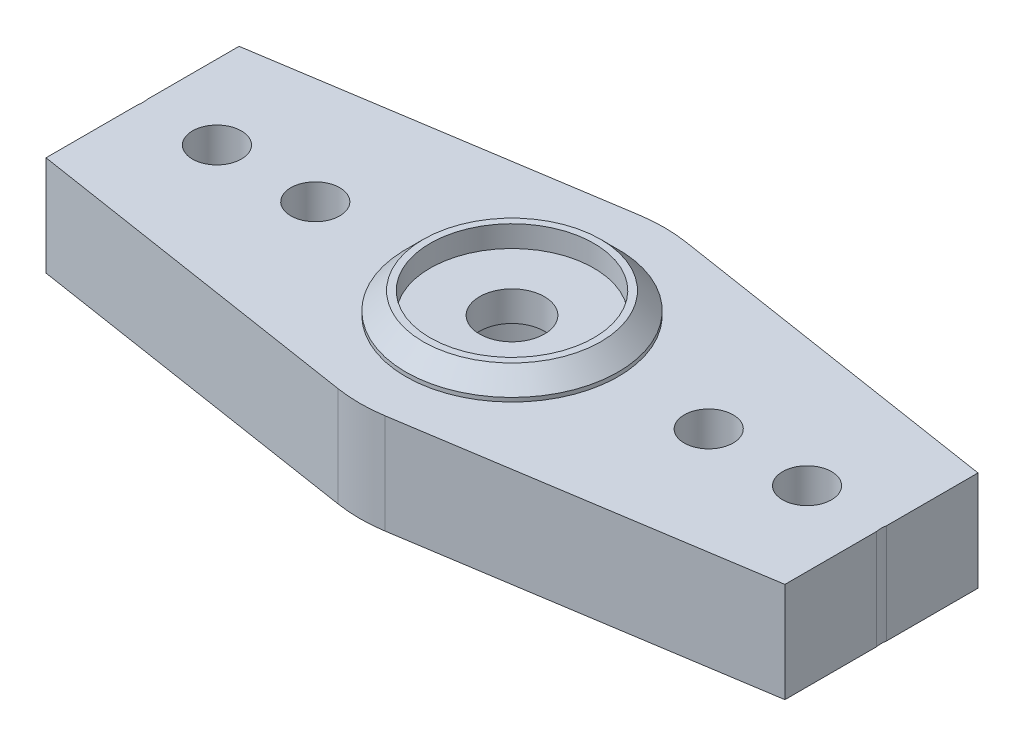
SolidWorks part; units mm, degrees
ref_plane "Front Plane" through (0, 0, 0) normal (0, 0, 1) x (1, 0, 0)
ref_plane "Top Plane" through (0, 0, 0) normal (0, 1, 0) x (1, 0, 0)
ref_plane "Right Plane" through (0, 0, 0) normal (1, 0, 0) x (0, 0, -1)
sketch "Sketch1" plane through (0, 0, 0) normal (0, 1, 0) x (1, 0, 0)
  line L0 (0, 0) -> (0, 10.1312) construction
  line L1 (0, 0) -> (-39.2364, 0) construction
  line L2 (-30.5039, 3.0869) -> (-1.1929, 7.6546)
  line L3 (-30.5039, -3.0869) -> (-1.1929, -7.6546)
  line L4 (0, 0) -> (0, -10.5582) construction
  line L5 (30.5039, -3.0869) -> (1.1929, -7.6546)
  line L6 (30.5039, 3.0869) -> (1.1929, 7.6546)
  circle A0 centre (0, 0) radius 1.651
  circle A1 centre (-10.0076, 0) radius 1.2446
  circle A2 centre (-15.0114, 0) radius 1.2446
  circle A3 centre (-20.0152, 0) radius 1.2446
  circle A4 centre (-25.019, 0) radius 1.2446
  circle A5 centre (-30.0228, 0) radius 1.2446
  arc A6 (-30.5039, 3.0869) -> (-30.5039, -3.0869) centre (-30.0228, 0) ccw
  arc A7 (-1.1929, -7.6546) -> (1.1929, -7.6546) centre (0, 0) ccw
  arc A8 (1.1929, 7.6546) -> (-1.1929, 7.6546) centre (0, 0) ccw
  arc A9 (30.5039, 3.0869) -> (30.5039, -3.0869) centre (30.0228, 0) cw
  circle A10 centre (30.0228, 0) radius 1.2446
  circle A11 centre (25.019, 0) radius 1.2446
  circle A12 centre (20.0152, 0) radius 1.2446
  circle A13 centre (15.0114, 0) radius 1.2446
  circle A14 centre (10.0076, 0) radius 1.2446
  dimension "D1" = 3.302
  dimension "D2" = 2.4892
  dimension "D5" = 2.4892
  dimension "D7" = 2.4892
  dimension "D10" = 2.4892
  dimension "D11" = 2.4892
  dimension "D12" = 6.2484
  dimension "D13" = 15.494
  dimension "D3" = 10.0076
  dimension "D4" = 5.0038
  dimension "D6" = 5.0038
  dimension "D8" = 5.0038
  dimension "D9" = 5.0038
extrude "Boss-Extrude1" add sketch "Sketch1" along normal blind 5.08
sketch "Sketch2" plane through (0, 5.08, 0) normal (0, 1, 0) x (1, 0, 0)
  circle A0 centre (0, 0) radius 5.4039
  circle A2 centre (0, 0) radius 4.1656
  dimension "D1" = 10.8077
  dimension "D2" = 8.3312
extrude "Boss-Extrude2" add sketch "Sketch2" along normal blind 1.0922
chamfer "Chamfer1" distance 0.889 angle 45 1 edges at (0, 6.1722, 5.4039)
sketch "Sketch4" plane through (0, 0, 0) normal (0, -1, 0) x (1, 0, 0)
  circle A0 centre (0, 0) radius 5.4102
  circle A1 centre (0, 0) radius 4.1656
  dimension "D1" = 10.8204
  dimension "D2" = 8.3312
extrude "Boss-Extrude3" add sketch "Sketch4" along normal blind 1.4986
chamfer "Chamfer2" distance 0.254 angle 45 1 edges at (0, -1.4986, -5.4102)
sketch "Sketch5" plane through (0, 5.08, 0) normal (0, 1, 0) x (1, 0, 0)
  line L0 (-18.796, 5.5085) -> (-18.796, -6.6581)
  line L1 (-18.796, 5.5085) -> (-33.9237, 5.5085)
  line L2 (-33.9237, 5.5085) -> (-33.9237, -6.6581)
  line L3 (-33.9237, -6.6581) -> (-18.796, -6.6581)
  line L4 (0, 10.0938) -> (0, -11.2969) construction
  line L5 (33.9237, -6.6581) -> (18.796, -6.6581)
  line L6 (33.9237, 5.5085) -> (33.9237, -6.6581)
  line L7 (18.796, 5.5085) -> (33.9237, 5.5085)
  line L8 (18.796, 5.5085) -> (18.796, -6.6581)
  circle A0 centre (-30.0228, 0) radius 1.2446 construction
  dimension "D1" = 18.796
  dimension "D2" = 15.1277
  dimension "D3" = 12.1666
  dimension "D4" = 5.5085
extrude "Cut-Extrude1" cut sketch "Sketch5" against normal through all
sketch "Sketch6" plane through (0, 0, 0) normal (0, -1, 0) x (1, 0, 0)
  circle A0 centre (0, 0) radius 4.1656
  dimension "D1" = 8.3312
extrude "Cut-Extrude2" cut sketch "Sketch6" against normal blind 3.556
